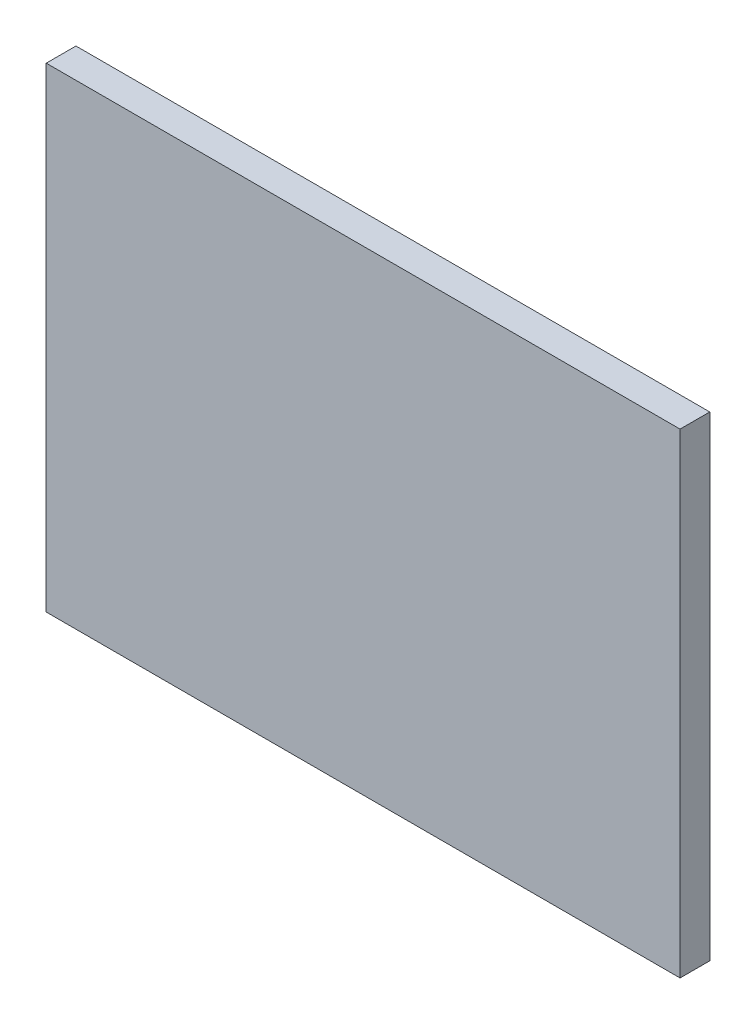
SolidWorks part; units mm, degrees
ref_plane "Front" through (0, 0, 0) normal (0, 0, 1) x (1, 0, 0)
ref_plane "Top" through (0, 0, 0) normal (0, 1, 0) x (1, 0, 0)
ref_plane "Right" through (0, 0, 0) normal (1, 0, 0) x (0, 0, -1)
sketch "Sketch1" plane through (0, 0, 0) normal (0, 0, 1) x (1, 0, 0)
  line L1 (-100.4004, -228.2088) -> (305.9996, -228.2088)
  line L2 (-100.4004, -228.2088) -> (-100.4004, 76.5912)
  line L3 (-100.4004, 76.5912) -> (305.9996, 76.5912)
  line L4 (305.9996, -228.2088) -> (305.9996, 76.5912)
  dimension "D1" = 406.4
  dimension "D2" = 304.8
extrude "Base-Extrude" add sketch "Sketch1" along normal blind 19.05
